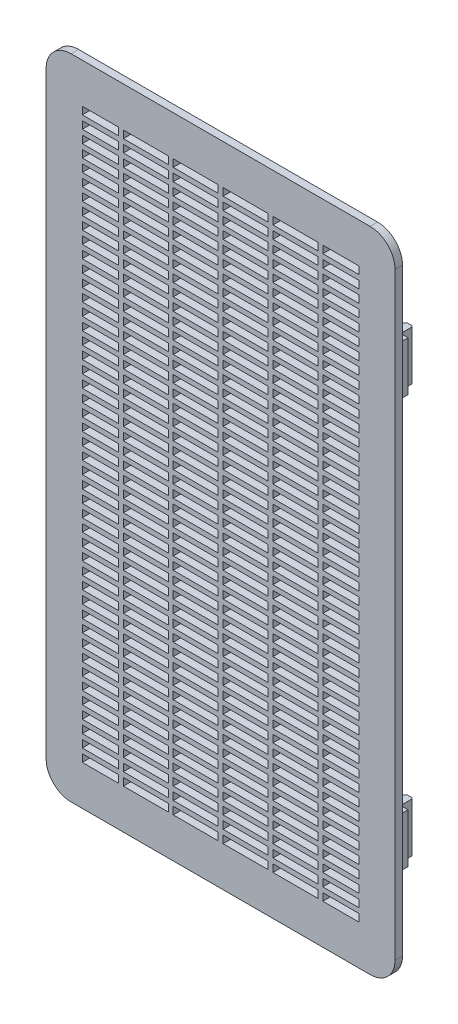
SolidWorks part; units mm, degrees
ref_plane "Front Plane" through (0, 0, 0) normal (0, 0, 1) x (1, 0, 0)
ref_plane "Top Plane" through (0, 0, 0) normal (0, 1, 0) x (1, 0, 0)
ref_plane "Right Plane" through (0, 0, 0) normal (1, 0, 0) x (0, 0, -1)
sketch "Sketch1" plane through (0, 0, 0) normal (0, 0, 1) x (1, 0, 0)
  line L1 (-70, -130) -> (70, -130)
  line L2 (-70, -130) -> (-70, 130)
  line L3 (-70, 130) -> (70, 130)
  line L4 (70, -130) -> (70, 130)
  line L5 (0, 130) -> (0, -130) construction
  line L6 (-70, 0) -> (70, 0) construction
  point P0 (0, 0)
  dimension "D1" = 140
  dimension "D2" = 260
extrude "Boss-Extrude1" add sketch "Sketch1" along normal blind 9
fillet "Fillet2" radius 10 4 edges at (-70, -130, 4.5) (70, -130, 4.5) (70, 130, 4.5) (-70, 130, 4.5)
sketch "Sketch3" plane through (0, 0, 9) normal (0, 0, 1) x (1, 0, 0)
  line L0 (60, 130) -> (-60, 130) construction
  line L1 (60.5, 121) -> (-60.5, 121)
  line L2 (60.5, 121) -> (60.5, -121)
  line L3 (60.5, -121) -> (-60.5, -121)
  line L4 (-60.5, 121) -> (-60.5, -121)
  line L5 (0, -121) -> (0, 121) construction
  line L6 (60.5, 0) -> (-60.5, 0) construction
  line L7 (-70, 120) -> (-70, -120) construction
  point P0 (0, 0)
  dimension "D1" = 9
  dimension "D2" = 9.5
extrude "Cut-Extrude1" cut sketch "Sketch3" against normal offset from surface (5 mm away) 4 up to face at (0, 0, 0)
sketch "Sketch8" plane through (0, 0, 0) normal (0, 0, -1) x (-1, 0, 0)
  line L0 (30, 0) -> (-30, 0) construction
  line L1 (-55.5, -116) -> (55.5, -116)
  line L2 (-55.5, -116) -> (-55.5, 116)
  line L3 (-55.5, 116) -> (55.5, 116)
  line L4 (55.5, -116) -> (55.5, 116)
  line L5 (0, 116) -> (0, -116) construction
  line L6 (-55.5, 0) -> (55.5, 0) construction
  line L7 (30, -10) -> (-30, -10) construction
  line L8 (30, 10) -> (-30, 10) construction
  arc A0 (30, -10) -> (30, 10) centre (30, 0) ccw construction
  arc A1 (-30, 10) -> (-30, -10) centre (-30, 0) ccw construction
  point P0 (0, 0)
  point P6 (0, 0)
  dimension "D3" = 10
  dimension "D1" = 111
  dimension "D2" = 232
  dimension "D4" = 60
extrude "Cut-Extrude2" cut sketch "Sketch8" against normal up to surface (4 mm away) up to face at (0, 0, 4)
sketch "Sketch9" plane through (0, 0, 0) normal (0, 0, -1) x (-1, 0, 0)
  line L0 (55.5, -116) -> (55.5, 116) construction
  line L1 (-55.5, 1) -> (55.5, 1) construction
  line L2 (-55.5, 1) -> (-55.5, -1) construction
  line L3 (-55.5, -1) -> (55.5, -1) construction
  line L4 (55.5, 1) -> (55.5, -1) construction
  line L5 (0, -1) -> (0, 1) construction
  line L6 (-55.5, 0) -> (55.5, 0) construction
  line L7 (-55.5, 6) -> (-55.5, 4)
  line L8 (-55.5, 6) -> (55.5, 6)
  line L9 (55.5, 6) -> (55.5, 4)
  line L10 (-55.5, 4) -> (55.5, 4)
  line L11 (-55.5, 11) -> (-55.5, 9)
  line L12 (-55.5, 11) -> (55.5, 11)
  line L13 (55.5, 11) -> (55.5, 9)
  line L14 (-55.5, 9) -> (55.5, 9)
  line L15 (-55.5, 16) -> (-55.5, 14)
  line L16 (-55.5, 16) -> (55.5, 16)
  line L17 (55.5, 16) -> (55.5, 14)
  line L18 (-55.5, 14) -> (55.5, 14)
  line L19 (-55.5, 21) -> (-55.5, 19)
  line L20 (-55.5, 21) -> (55.5, 21)
  line L21 (55.5, 21) -> (55.5, 19)
  line L22 (-55.5, 19) -> (55.5, 19)
  line L23 (-55.5, 26) -> (-55.5, 24)
  line L24 (-55.5, 26) -> (55.5, 26)
  line L25 (55.5, 26) -> (55.5, 24)
  line L26 (-55.5, 24) -> (55.5, 24)
  line L27 (-55.5, 31) -> (-55.5, 29)
  line L28 (-55.5, 31) -> (55.5, 31)
  line L29 (55.5, 31) -> (55.5, 29)
  line L30 (-55.5, 29) -> (55.5, 29)
  line L31 (-55.5, 36) -> (-55.5, 34)
  line L32 (-55.5, 36) -> (55.5, 36)
  line L33 (55.5, 36) -> (55.5, 34)
  line L34 (-55.5, 34) -> (55.5, 34)
  line L35 (-55.5, 41) -> (-55.5, 39)
  line L36 (-55.5, 41) -> (55.5, 41)
  line L37 (55.5, 41) -> (55.5, 39)
  line L38 (-55.5, 39) -> (55.5, 39)
  line L39 (-55.5, 46) -> (-55.5, 44)
  line L40 (-55.5, 46) -> (55.5, 46)
  line L41 (55.5, 46) -> (55.5, 44)
  line L42 (-55.5, 44) -> (55.5, 44)
  line L43 (-55.5, 51) -> (-55.5, 49)
  line L44 (-55.5, 51) -> (55.5, 51)
  line L45 (55.5, 51) -> (55.5, 49)
  line L46 (-55.5, 49) -> (55.5, 49)
  line L47 (-55.5, 56) -> (-55.5, 54)
  line L48 (-55.5, 56) -> (55.5, 56)
  line L49 (55.5, 56) -> (55.5, 54)
  line L50 (-55.5, 54) -> (55.5, 54)
  line L51 (-55.5, 61) -> (-55.5, 59)
  line L52 (-55.5, 61) -> (55.5, 61)
  line L53 (55.5, 61) -> (55.5, 59)
  line L54 (-55.5, 59) -> (55.5, 59)
  line L55 (-55.5, 66) -> (-55.5, 64)
  line L56 (-55.5, 66) -> (55.5, 66)
  line L57 (55.5, 66) -> (55.5, 64)
  line L58 (-55.5, 64) -> (55.5, 64)
  line L59 (-55.5, 71) -> (-55.5, 69)
  line L60 (-55.5, 71) -> (55.5, 71)
  line L61 (55.5, 71) -> (55.5, 69)
  line L62 (-55.5, 69) -> (55.5, 69)
  line L63 (-55.5, 76) -> (-55.5, 74)
  line L64 (-55.5, 76) -> (55.5, 76)
  line L65 (55.5, 76) -> (55.5, 74)
  line L66 (-55.5, 74) -> (55.5, 74)
  line L67 (-55.5, 81) -> (-55.5, 79)
  line L68 (-55.5, 81) -> (55.5, 81)
  line L69 (55.5, 81) -> (55.5, 79)
  line L70 (-55.5, 79) -> (55.5, 79)
  line L71 (-55.5, 86) -> (-55.5, 84)
  line L72 (-55.5, 86) -> (55.5, 86)
  line L73 (55.5, 86) -> (55.5, 84)
  line L74 (-55.5, 84) -> (55.5, 84)
  line L75 (-55.5, 91) -> (-55.5, 89)
  line L76 (-55.5, 91) -> (55.5, 91)
  line L77 (55.5, 91) -> (55.5, 89)
  line L78 (-55.5, 89) -> (55.5, 89)
  line L79 (-55.5, 96) -> (-55.5, 94)
  line L80 (-55.5, 96) -> (55.5, 96)
  line L81 (55.5, 96) -> (55.5, 94)
  line L82 (-55.5, 94) -> (55.5, 94)
  line L83 (-55.5, 101) -> (-55.5, 99)
  line L84 (-55.5, 101) -> (55.5, 101)
  line L85 (55.5, 101) -> (55.5, 99)
  line L86 (-55.5, 99) -> (55.5, 99)
  line L87 (-55.5, 106) -> (-55.5, 104)
  line L88 (-55.5, 106) -> (55.5, 106)
  line L89 (55.5, 106) -> (55.5, 104)
  line L90 (-55.5, 104) -> (55.5, 104)
  line L91 (-55.5, 111) -> (-55.5, 109)
  line L92 (-55.5, 111) -> (55.5, 111)
  line L93 (55.5, 111) -> (55.5, 109)
  line L94 (-55.5, 109) -> (55.5, 109)
  line L95 (-55.5, 116) -> (-55.5, 114)
  line L96 (-55.5, 116) -> (55.5, 116)
  line L97 (55.5, 116) -> (55.5, 114)
  line L98 (-55.5, 114) -> (55.5, 114)
  line L99 (-55.5, -4) -> (-55.5, -6)
  line L100 (-55.5, -4) -> (55.5, -4)
  line L101 (55.5, -4) -> (55.5, -6)
  line L102 (-55.5, -6) -> (55.5, -6)
  line L103 (-55.5, -9) -> (-55.5, -11)
  line L104 (-55.5, -9) -> (55.5, -9)
  line L105 (55.5, -9) -> (55.5, -11)
  line L106 (-55.5, -11) -> (55.5, -11)
  line L107 (-55.5, -14) -> (-55.5, -16)
  line L108 (-55.5, -14) -> (55.5, -14)
  line L109 (55.5, -14) -> (55.5, -16)
  line L110 (-55.5, -16) -> (55.5, -16)
  line L111 (-55.5, -19) -> (-55.5, -21)
  line L112 (-55.5, -19) -> (55.5, -19)
  line L113 (55.5, -19) -> (55.5, -21)
  line L114 (-55.5, -21) -> (55.5, -21)
  line L115 (-55.5, -24) -> (-55.5, -26)
  line L116 (-55.5, -24) -> (55.5, -24)
  line L117 (55.5, -24) -> (55.5, -26)
  line L118 (-55.5, -26) -> (55.5, -26)
  line L119 (-55.5, -29) -> (-55.5, -31)
  line L120 (-55.5, -29) -> (55.5, -29)
  line L121 (55.5, -29) -> (55.5, -31)
  line L122 (-55.5, -31) -> (55.5, -31)
  line L123 (-55.5, -34) -> (-55.5, -36)
  line L124 (-55.5, -34) -> (55.5, -34)
  line L125 (55.5, -34) -> (55.5, -36)
  line L126 (-55.5, -36) -> (55.5, -36)
  line L127 (-55.5, -39) -> (-55.5, -41)
  line L128 (-55.5, -39) -> (55.5, -39)
  line L129 (55.5, -39) -> (55.5, -41)
  line L130 (-55.5, -41) -> (55.5, -41)
  line L131 (-55.5, -44) -> (-55.5, -46)
  line L132 (-55.5, -44) -> (55.5, -44)
  line L133 (55.5, -44) -> (55.5, -46)
  line L134 (-55.5, -46) -> (55.5, -46)
  line L135 (-55.5, -49) -> (-55.5, -51)
  line L136 (-55.5, -49) -> (55.5, -49)
  line L137 (55.5, -49) -> (55.5, -51)
  line L138 (-55.5, -51) -> (55.5, -51)
  line L139 (-55.5, -54) -> (-55.5, -56)
  line L140 (-55.5, -54) -> (55.5, -54)
  line L141 (55.5, -54) -> (55.5, -56)
  line L142 (-55.5, -56) -> (55.5, -56)
  line L143 (-55.5, -59) -> (-55.5, -61)
  line L144 (-55.5, -59) -> (55.5, -59)
  line L145 (55.5, -59) -> (55.5, -61)
  line L146 (-55.5, -61) -> (55.5, -61)
  line L147 (-55.5, -64) -> (-55.5, -66)
  line L148 (-55.5, -64) -> (55.5, -64)
  line L149 (55.5, -64) -> (55.5, -66)
  line L150 (-55.5, -66) -> (55.5, -66)
  line L151 (-55.5, -69) -> (-55.5, -71)
  line L152 (-55.5, -69) -> (55.5, -69)
  line L153 (55.5, -69) -> (55.5, -71)
  line L154 (-55.5, -71) -> (55.5, -71)
  line L155 (-55.5, -74) -> (-55.5, -76)
  line L156 (-55.5, -74) -> (55.5, -74)
  line L157 (55.5, -74) -> (55.5, -76)
  line L158 (-55.5, -76) -> (55.5, -76)
  line L159 (-55.5, -79) -> (-55.5, -81)
  line L160 (-55.5, -79) -> (55.5, -79)
  line L161 (55.5, -79) -> (55.5, -81)
  line L162 (-55.5, -81) -> (55.5, -81)
  line L163 (-55.5, -84) -> (-55.5, -86)
  line L164 (-55.5, -84) -> (55.5, -84)
  line L165 (55.5, -84) -> (55.5, -86)
  line L166 (-55.5, -86) -> (55.5, -86)
  line L167 (-55.5, -89) -> (-55.5, -91)
  line L168 (-55.5, -89) -> (55.5, -89)
  line L169 (55.5, -89) -> (55.5, -91)
  line L170 (-55.5, -91) -> (55.5, -91)
  line L171 (-55.5, -94) -> (-55.5, -96)
  line L172 (-55.5, -94) -> (55.5, -94)
  line L173 (55.5, -94) -> (55.5, -96)
  line L174 (-55.5, -96) -> (55.5, -96)
  line L175 (-55.5, -99) -> (-55.5, -101)
  line L176 (-55.5, -99) -> (55.5, -99)
  line L177 (55.5, -99) -> (55.5, -101)
  line L178 (-55.5, -101) -> (55.5, -101)
  line L179 (-55.5, -104) -> (-55.5, -106)
  line L180 (-55.5, -104) -> (55.5, -104)
  line L181 (55.5, -104) -> (55.5, -106)
  line L182 (-55.5, -106) -> (55.5, -106)
  line L183 (-55.5, -109) -> (-55.5, -111)
  line L184 (-55.5, -109) -> (55.5, -109)
  line L185 (55.5, -109) -> (55.5, -111)
  line L186 (-55.5, -111) -> (55.5, -111)
  line L187 (-55.5, -114) -> (-55.5, -116)
  line L188 (-55.5, -114) -> (55.5, -114)
  line L189 (55.5, -114) -> (55.5, -116)
  line L190 (-55.5, -116) -> (55.5, -116)
  line L192 (-55.5, 1) -> (34.8738, 1)
  line L193 (-55.5, 1) -> (-55.5, -1)
  line L194 (-55.5, -1) -> (34.8738, -1)
  line L196 (-10.3131, -1) -> (-10.3131, 1) construction
  line L197 (-55.5, 0) -> (-27.0207, 0) construction
  line L198 (55.5, 1) -> (34.8738, 1)
  line L199 (55.5, 1) -> (55.5, -1)
  line L200 (55.5, -1) -> (34.8738, -1)
  line L202 (45.1869, -1) -> (45.1869, 1) construction
  line L203 (55.5, 0) -> (34.8738, 0) construction
  point P0 (0, 0)
  point P378 (-10.3131, 0)
  point P481 (45.1869, 0)
  dimension "D1" = 2
  dimension "D2" = 24
  dimension "D3" = 24
extrude "Boss-Extrude3" add sketch "Sketch9" against normal up to surface (4 mm away) up to face at (0, 0, 4)
sketch "Sketch10" plane through (0, 0, 0) normal (0, 0, -1) x (-1, 0, 0)
  line L0 (-55.5, 114) -> (55.5, 114) construction
  line L1 (-1, -114) -> (1, -114)
  line L2 (-1, -114) -> (-1, 114)
  line L3 (-1, 114) -> (1, 114)
  line L4 (1, -114) -> (1, 114)
  line L5 (0, 114) -> (0, -114) construction
  line L6 (-1, 0) -> (1, 0) construction
  line L7 (19, -114) -> (19, 114)
  line L8 (19, -114) -> (21, -114)
  line L9 (21, -114) -> (21, 114)
  line L10 (19, 114) -> (21, 114)
  line L11 (39, -114) -> (39, 114)
  line L12 (39, -114) -> (41, -114)
  line L13 (41, -114) -> (41, 114)
  line L14 (39, 114) -> (41, 114)
  line L15 (-21, -114) -> (-21, 114)
  line L16 (-21, -114) -> (-19, -114)
  line L17 (-19, -114) -> (-19, 114)
  line L18 (-21, 114) -> (-19, 114)
  line L19 (-41, -114) -> (-41, 114)
  line L20 (-41, -114) -> (-39, -114)
  line L21 (-39, -114) -> (-39, 114)
  line L22 (-41, 114) -> (-39, 114)
  point P0 (0, 0)
  point P27 (-21, 6.7097)
  point P28 (-21, -8.1301)
  point P29 (-19, -8.1301)
  point P30 (-19, 6.7097)
  dimension "D1" = 2
  dimension "D4" = 20
  dimension "D2" = 3
  dimension "D3" = 3
extrude "Boss-Extrude4" add sketch "Sketch10" against normal up to surface (4 mm away) up to face at (0, -112.5, 4)
sketch "Sketch11" plane through (0, 0, 9) normal (0, 0, 1) x (1, 0, 0)
  line L1 (-80.179, -138.2931) -> (80.179, -138.2931)
  line L2 (-80.179, -138.2931) -> (-80.179, 138.2931)
  line L3 (-80.179, 138.2931) -> (80.179, 138.2931)
  line L4 (80.179, -138.2931) -> (80.179, 138.2931)
  line L5 (0, 138.2931) -> (0, -138.2931) construction
  line L6 (-80.179, 0) -> (80.179, 0) construction
  point P0 (0, 0)
extrude "Cut-Extrude3" cut sketch "Sketch11" against normal offset from surface (6 mm away) 3 up to face at (30, -107.5, 0)
ref_plane "Plane1" through (0, 82, 0) normal (0, 1, 0) x (1, 0, 0)
sketch "Sketch12" plane through (0, 82, 0) normal (0, 1, 0) x (1, 0, 0)
  line L0 (-59.8008, 0) -> (-59.8008, 4)
  line L1 (-60, 0) -> (-70, 0) construction
  line L3 (-65.25, 4) -> (-65.25, 9)
  line L4 (-65.25, 9) -> (-62.75, 9)
  line L5 (-62.75, 9) -> (-61.25, 6.5)
  line L6 (-61.25, 6.5) -> (-62.75, 4)
  line L8 (-68.1992, 4) -> (-68.1992, 0)
  line L9 (60, 0) -> (-60, 0) construction
  line L10 (-68.1992, 0) -> (-59.8008, 0)
  line L11 (-62.75, 9) -> (-62.75, 4) construction
  line L12 (-64, 9) -> (-64, 0) construction
  line L13 (-70, -3) -> (-70, 0) construction
  line L14 (0, 0) -> (0, 28.9486) construction
  line L15 (-68.1992, 4) -> (-65.25, 4)
  line L16 (-62.75, 4) -> (-59.8008, 4)
  line L17 (61.25, 6.5) -> (62.75, 4)
  line L18 (62.75, 9) -> (61.25, 6.5)
  line L19 (65.25, 9) -> (62.75, 9)
  line L20 (65.25, 4) -> (65.25, 9)
  line L21 (68.1992, 4) -> (65.25, 4)
  line L22 (68.1992, 4) -> (68.1992, 0)
  line L23 (68.1992, 0) -> (59.8008, 0)
  line L24 (59.8008, 0) -> (59.8008, 4)
  line L25 (62.75, 4) -> (59.8008, 4)
  dimension "D1" = 2.5
  dimension "D2" = 1.5
  dimension "D3" = 5
  dimension "D4" = 4
  dimension "D5" = 6
  dimension "D6" = 8.3983
extrude "Boss-Extrude5" add sketch "Sketch12" along normal mid plane 19.8
mirror "Mirror1" about plane through (0, 0, 0) normal (0, 1, 0) of "Boss-Extrude5"
chamfer "Chamfer1" distance 0.5 angle 45 4 edges at (-65.25, 82, -9) (65.25, -82, -9) (65.25, 82, -9) (-65.25, -82, -9)
fillet "Fillet3" radius 1 4 edges at (65.25, 82, -4) (65.25, -82, -4) (-65.25, 82, -4) (-65.25, -82, -4)
